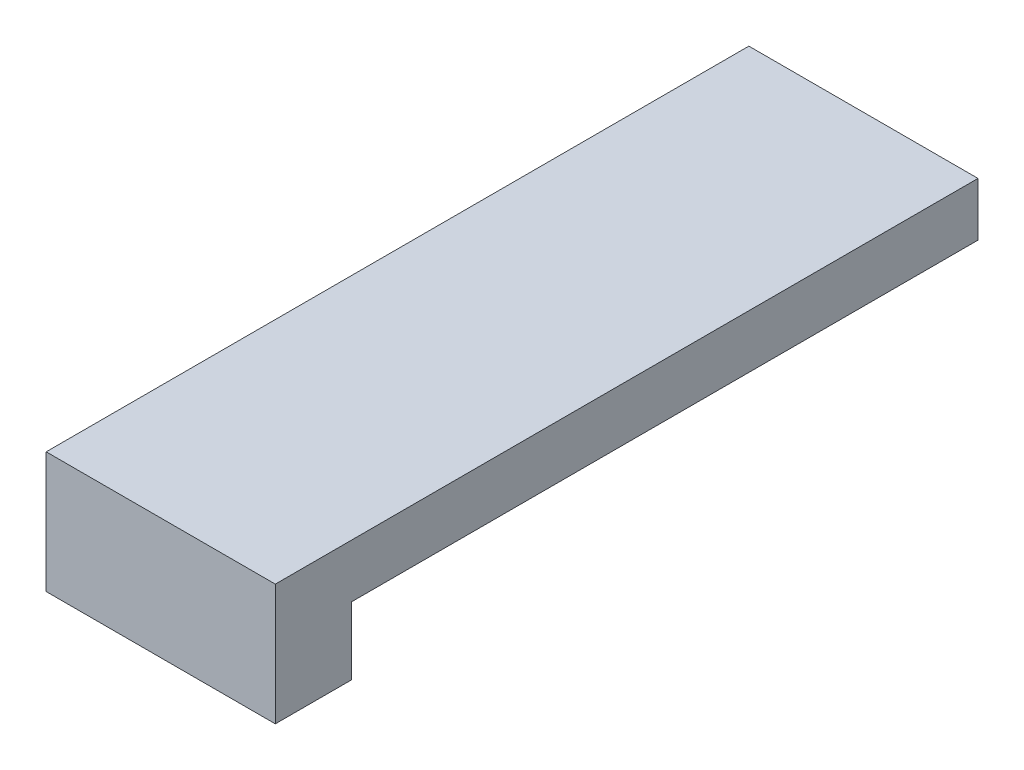
SolidWorks part; units mm, degrees
ref_plane "Alzado" through (0, 0, 0) normal (0, 0, 1) x (1, 0, 0)
ref_plane "Planta" through (0, 0, 0) normal (0, 1, 0) x (1, 0, 0)
ref_plane "Vista lateral" through (0, 0, 0) normal (1, 0, 0) x (0, 0, -1)
sketch "Croquis1" plane through (0, 0, 0) normal (0, 0, 1) x (1, 0, 0)
  line L0 (-31.0896, 25.0532) -> (-16.0896, 25.0532)
  line L1 (-16.0896, 25.0532) -> (-16.0896, 21.5532)
  line L2 (-16.0896, 21.5532) -> (-31.0896, 21.5532)
  line L3 (-31.0896, 21.5532) -> (-31.0896, 25.0532)
extrude "Saliente-Extruir1" add sketch "Croquis1" along normal blind 41
sketch "Croquis2" plane through (0, 0, 41) normal (0, 0, 1) x (1, 0, 0)
  line L0 (-31.0896, 25.0532) -> (-31.1015, 17.129)
  line L1 (-16.0896, 25.0532) -> (-16.0896, 17.129)
  line L2 (-16.0896, 17.129) -> (-31.1015, 17.129)
  line L3 (-16.0896, 25.0532) -> (-31.0896, 25.0532)
extrude "Saliente-Extruir3" add sketch "Croquis2" along normal blind 5
